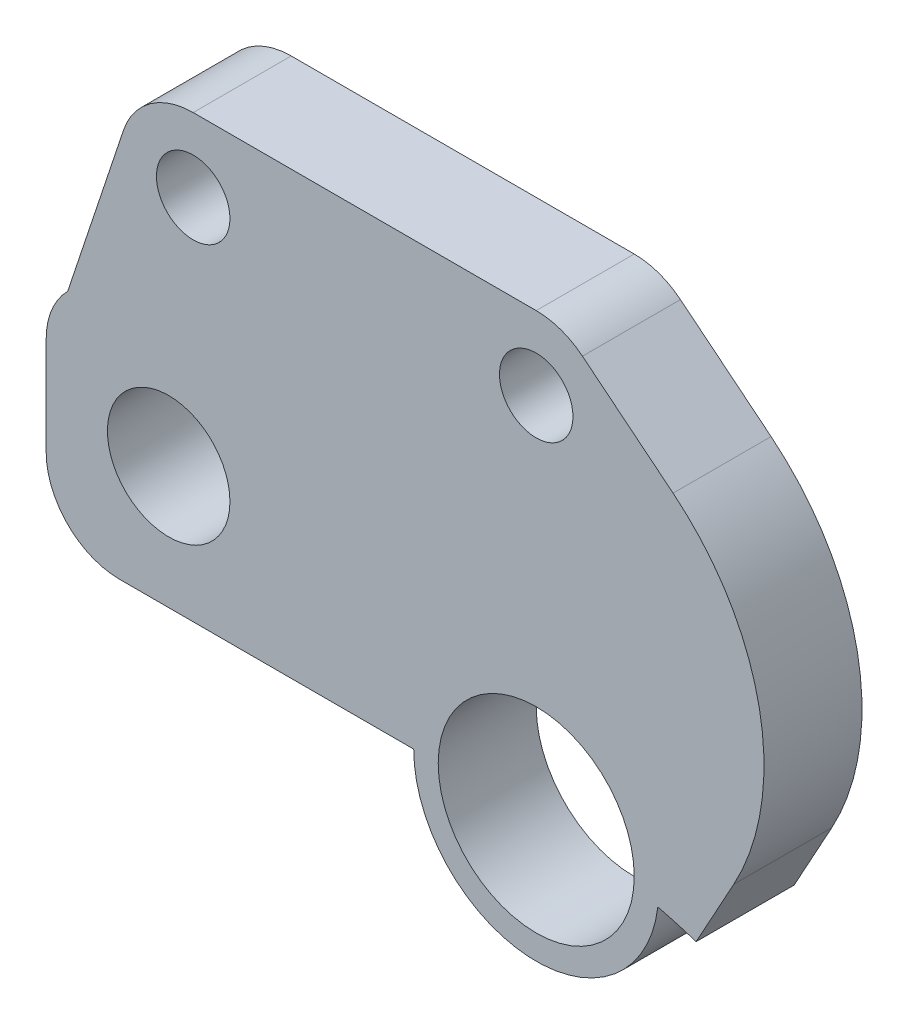
SolidWorks part; units mm, degrees
ref_plane "Alzado" through (0, 0, 0) normal (0, 0, 1) x (1, 0, 0)
ref_plane "Planta" through (0, 0, 0) normal (0, 1, 0) x (1, 0, 0)
ref_plane "Vista lateral" through (0, 0, 0) normal (1, 0, 0) x (0, 0, -1)
sketch "Croquis1" plane through (0, 0, 0) normal (0, 0, 1) x (1, 0, 0)
  line L0 (0, 0) -> (0, -20.95) construction
  line L1 (0, 0) -> (0, 20.95) construction
  line L2 (-20, 25.95) -> (-15, 25.95) construction
  line L3 (0, 20.95) -> (-4, 20.95)
  line L4 (0, 20.95) -> (0, 24.95)
  line L5 (0, 30.95) -> (-17, 30.95)
  line L6 (-20, 23.95) -> (-20, 27.95)
  line L7 (0, -25.95) -> (15.9531, -25.95)
  line L8 (-5, 20.95) -> (-17, 20.95)
  line L9 (0, 0) -> (18.3494, 18.3494) construction
  line L10 (0, 0) -> (25.95, 0) construction
  line L11 (-14, 30.95) -> (-14, 32.95) construction
  line L12 (0, 30.95) -> (0, 35.95) construction
  line L13 (0, 35.95) -> (-14, 35.95) construction
  line L14 (-16.8461, 36.8985) -> (-19.1213, 30.0713)
  line L15 (-14, 38.95) -> (0, 38.95)
  line L16 (1.8868, 38.2824) -> (19.4651, 24.0627)
  line L17 (-14, 34.45) -> (-14, 35.95) construction
  arc A0 (-3.9817, -20.5681) -> (3.9817, -20.5681) centre (0, 0) ccw
  arc A1 (17.6654, -25.4133) -> (0, 30.95) centre (0, 0) ccw
  arc A2 (-5, 20.95) -> (4.9643, 20.3533) centre (0, 20.95) ccw
  arc A3 (4.9643, -20.3533) -> (0, -25.95) centre (0, -20.95) ccw
  circle A4 centre (0, 20.95) radius 4
  circle A5 centre (0, -20.95) radius 4
  circle A6 centre (-15, 25.95) radius 2.5
  circle A7 centre (0, 0) radius 25.95 construction
  arc A8 (4.9643, -20.3533) -> (4.9643, 20.3533) centre (0, 0) ccw
  circle A9 centre (18.3494, 18.3494) radius 2
  circle A10 centre (25.95, 0) radius 2
  arc A11 (15.9531, -25.95) -> (17.6654, -25.4133) centre (15.9531, -22.95) ccw
  arc A12 (-17, 20.95) -> (-20, 23.95) centre (-17, 23.95) cw
  arc A13 (-17, 30.95) -> (-20, 27.95) centre (-17, 27.95) ccw
  circle A14 centre (-14, 35.95) radius 1.5
  circle A15 centre (0, 35.95) radius 1.5
  arc A16 (-14, 38.95) -> (-16.8461, 36.8985) centre (-14, 35.95) ccw
  arc A17 (1.8868, 38.2824) -> (0, 38.95) centre (0, 35.95) ccw
  arc A18 (13.1759, 16.288) -> (19.4651, 24.0627) centre (16.3205, 20.1753) ccw
  point P32 (-20, 30.95)
  dimension "D1" = 41.9
  dimension "D3" = 10
  dimension "D4" = 10
  dimension "D5" = 10
  dimension "D6" = 8
  dimension "D7" = 8
  dimension "D9" = 5
  dimension "D12" = 5
  dimension "D13" = 4
  dimension "D14" = 4
  dimension "D17" = 3
  dimension "D18" = 5
  dimension "D19" = 3
  dimension "D20" = 3
  dimension "D22" = 6
  dimension "D2" = 180
  dimension "D8" = 20
  dimension "D10" = 5
  dimension "D11" = 90
  dimension "D15" = 45
  dimension "D16" = 45
  dimension "D21" = 6
extrude "Saliente-Extruir1" add sketch "Croquis1" along normal blind 4 contours A8 A3 L7 A1 L5 L6 L8 A2 A6 A5 A4 | L16 A17 L15 A16 L14 A13 L5 A1 A14 A15 | A9
sketch "Croquis2" plane through (0, 0, 4) normal (0, 0, 1) x (1, 0, 0)
  line L0 (6.5263, 19.9075) -> (12.0871, 30.031)
  line L1 (1.8868, 38.2824) -> (19.4651, 24.0627) construction
  line L7 (19.4651, 24.0627) -> (1.8868, 38.2824)
  line L8 (0, 38.95) -> (-14, 38.95)
  line L9 (-16.8461, 36.8985) -> (-19.1213, 30.0713)
  line L10 (-20, 27.95) -> (-20, 23.95)
  line L11 (-17, 20.95) -> (-5, 20.95)
  line L12 (19.4651, 24.0627) -> (1.8868, 38.2824)
  line L13 (0, 38.95) -> (-14, 38.95)
  line L14 (-16.8461, 36.8985) -> (-19.1213, 30.0713)
  line L15 (-20, 27.95) -> (-20, 23.95)
  line L16 (-17, 20.95) -> (-5, 20.95)
  arc A0 (13.1759, 16.288) -> (4.9643, 20.3533) centre (0, 0) ccw construction
  arc A8 (13.1759, 16.288) -> (4.9643, 20.3533) centre (0, 0) ccw
  arc A9 (13.1759, 16.288) -> (19.4651, 24.0627) centre (16.3205, 20.1753) ccw
  arc A10 (1.8868, 38.2824) -> (0, 38.95) centre (0, 35.95) ccw
  arc A11 (-14, 38.95) -> (-16.8461, 36.8985) centre (-14, 35.95) ccw
  arc A12 (-19.1213, 30.0713) -> (-20, 27.95) centre (-17, 27.95) ccw
  arc A13 (-20, 23.95) -> (-17, 20.95) centre (-17, 23.95) ccw
  arc A14 (-5, 20.95) -> (4.9643, 20.3533) centre (0, 20.95) ccw
  arc A15 (13.1759, 16.288) -> (4.9643, 20.3533) centre (0, 0) ccw
  arc A16 (13.1759, 16.288) -> (19.4651, 24.0627) centre (16.3205, 20.1753) ccw
  arc A17 (1.8868, 38.2824) -> (0, 38.95) centre (0, 35.95) ccw
  arc A18 (-14, 38.95) -> (-16.8461, 36.8985) centre (-14, 35.95) ccw
  arc A19 (-19.1213, 30.0713) -> (-20, 27.95) centre (-17, 27.95) ccw
  arc A20 (-20, 23.95) -> (-17, 20.95) centre (-17, 23.95) ccw
  arc A21 (-5, 20.95) -> (4.9643, 20.3533) centre (0, 20.95) ccw
  arc M16 (4.9643, 20.3533) -> (13.1759, 16.288) centre (0, 0) cw
  arc M17 (13.1759, 16.288) -> (19.4651, 24.0627) centre (16.3205, 20.1753) ccw
  line M18 (19.4651, 24.0627) -> (1.8868, 38.2824)
  dimension "D1" = 0
extrude "Cortar-Extruir1" cut sketch "Croquis2" against normal blind 10 contours L0 M16 M17 M18
fillet "Redondeo1" radius 10 1 edges at (12.0871, 30.031, 2)
